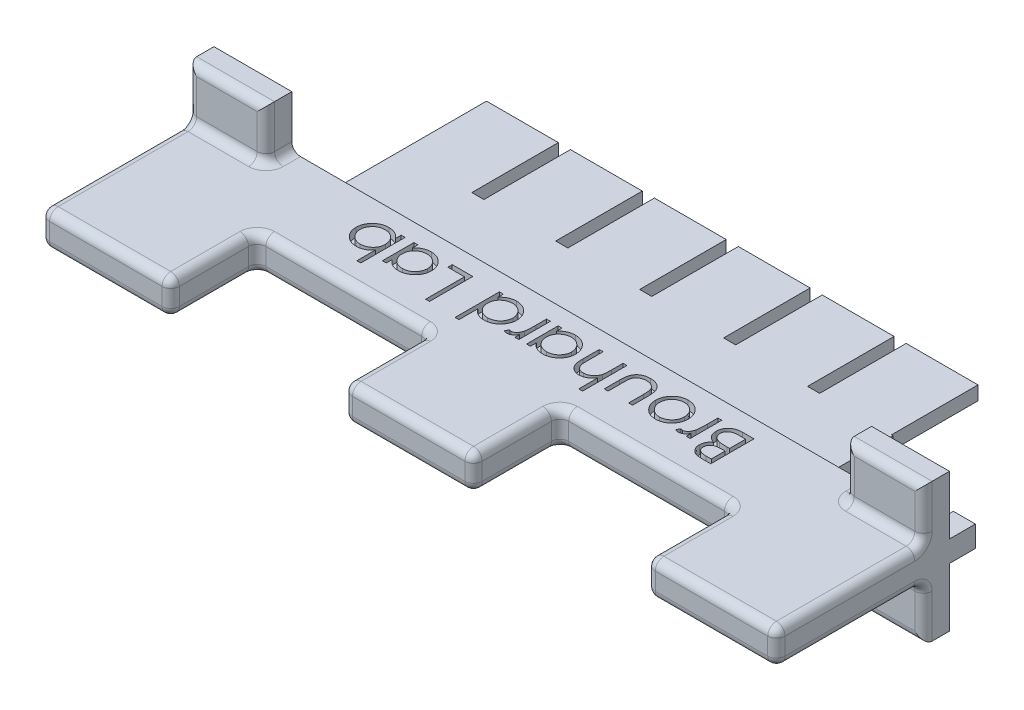
SolidWorks part; units mm, degrees
ref_plane "Front Plane" through (0, 0, 0) normal (0, 0, 1) x (1, 0, 0)
ref_plane "Top Plane" through (0, 0, 0) normal (0, 1, 0) x (1, 0, 0)
ref_plane "Right Plane" through (0, 0, 0) normal (1, 0, 0) x (0, 0, -1)
sketch "Sketch1" plane through (0, 0, 0) normal (0, 0, 1) x (1, 0, 0)
  line L1 (-42.5, 2) -> (42.5, 2)
  line L2 (-42.5, 2) -> (-42.5, -2)
  line L3 (-42.5, -2) -> (42.5, -2)
  line L4 (42.5, 2) -> (42.5, -2)
  line L5 (-42.5, 2) -> (42.5, -2) construction
  line L6 (-42.5, -2) -> (42.5, 2) construction
  point P0 (0, 0)
  dimension "D1" = 85
  dimension "D2" = 4
extrude "Boss-Extrude1" add sketch "Sketch1" along normal blind 10
sketch "Sketch2" plane through (0, 0, 10) normal (0, 0, 1) x (1, 0, 0)
  line L0 (-42.5, -2) -> (42.5, -2) construction
  line L1 (-42.5, 2) -> (-27.5, 2)
  line L2 (-42.5, 2) -> (-42.5, -2)
  line L3 (-42.5, -2) -> (-27.5, -2)
  line L4 (-27.5, 2) -> (-27.5, -2)
  line L6 (42.5, 2) -> (27.5, 2)
  line L7 (42.5, 2) -> (42.5, -2)
  line L8 (42.5, -2) -> (27.5, -2)
  line L9 (27.5, 2) -> (27.5, -2)
  line L10 (-7.5, 2) -> (7.5, 2)
  line L11 (-7.5, 2) -> (-7.5, -2)
  line L12 (-7.5, -2) -> (7.5, -2)
  line L13 (7.5, 2) -> (7.5, -2)
  line L14 (-7.5, 2) -> (7.5, -2) construction
  line L15 (-7.5, -2) -> (7.5, 2) construction
  point P12 (0, 0)
  dimension "D1" = 15
extrude "Boss-Extrude2" add sketch "Sketch2" along normal blind 10
sketch "Sketch3" plane through (0, 0, 0) normal (0, 0, -1) x (-1, 0, 0)
  line L9 (42.5, -1.225) -> (39.95, -1.225)
  line L10 (42.5, -1.225) -> (42.5, 1.225)
  line L11 (42.5, 1.225) -> (39.95, 1.225)
  line L12 (39.95, -1.225) -> (39.95, 1.225)
  line L13 (42.5, -1.225) -> (39.95, 1.225) construction
  line L14 (42.5, 1.225) -> (39.95, -1.225) construction
  line L15 (42.5, 2) -> (42.5, -2) construction
  line L16 (0, 0) -> (0, 13.9589)
  line L17 (-42.5, 1.225) -> (-39.95, -1.225) construction
  line L18 (-42.5, -1.225) -> (-39.95, 1.225) construction
  line L19 (-39.95, -1.225) -> (-39.95, 1.225)
  line L20 (-42.5, 1.225) -> (-39.95, 1.225)
  line L21 (-42.5, -1.225) -> (-42.5, 1.225)
  line L22 (-42.5, -1.225) -> (-39.95, -1.225)
  point P3 (42.5, 0)
  point P10 (41.225, 0)
  point P16 (-41.225, 0)
  line M3 (-42.5, 2) -> (-42.5, -2)
  dimension "D1" = 2.45
  dimension "D2" = 2.55
extrude "Boss-Extrude3" add sketch "Sketch3" along normal blind 3 contours L22 L19 L20 M3 | L12 L11 L10 L9
sketch "Sketch4" plane through (0, 0, 0) normal (0, 0, -1) x (-1, 0, 0)
  line L1 (28.5, -0.8) -> (-28.5, -0.8)
  line L2 (28.5, -0.8) -> (28.5, 0.8)
  line L3 (28.5, 0.8) -> (-28.5, 0.8)
  line L4 (-28.5, -0.8) -> (-28.5, 0.8)
  line L5 (28.5, -0.8) -> (-28.5, 0.8) construction
  line L6 (28.5, 0.8) -> (-28.5, -0.8) construction
  point P0 (0, 0)
  dimension "D1" = 1.6
  dimension "D2" = 57
extrude "Boss-Extrude4" add sketch "Sketch4" along normal blind 7.5
sketch "Sketch6" plane through (0, 0, 0) normal (0, 0, -1) x (-1, 0, 0)
  line L1 (42.5, -2) -> (33.5, -2)
  line L2 (42.5, -2) -> (42.5, -8)
  line L3 (42.5, -8) -> (33.5, -8)
  line L4 (33.5, -2) -> (33.5, -8)
  line L5 (42.5, 2) -> (33.5, 2)
  line L6 (42.5, 2) -> (42.5, 8)
  line L7 (42.5, 8) -> (33.5, 8)
  line L8 (33.5, 2) -> (33.5, 8)
  line L9 (-42.5, -2) -> (-33.5, -2)
  line L10 (-42.5, -2) -> (-42.5, -8)
  line L11 (-42.5, -8) -> (-33.5, -8)
  line L12 (-33.5, -2) -> (-33.5, -8)
  line L13 (-42.5, 2) -> (-33.5, 2)
  line L14 (-42.5, 2) -> (-42.5, 8)
  line L15 (-42.5, 8) -> (-33.5, 8)
  line L16 (-33.5, 2) -> (-33.5, 8)
  dimension "D1" = 6
  dimension "D2" = 9
extrude "Boss-Extrude6" add sketch "Sketch6" against normal blind 3
fillet "Fillet1" radius 1 52 edges at (-42.5, -2, 11.5) (-33.5, -2, 1.5) (-38, -2, 3) (-33.5, -5, 3) (-38, -8, 3) (-42.5, -5, 3) (-27.5, 0, 20) (-35, -2, 20) (-42.5, 0, 20) (-35, 2, 20) (33.5, -2, 1.5) (42.5, -2, 11.5) (42.5, 2, 11.5) (33.5, 2, 1.5) (-33.5, 2, 1.5) (-42.5, 2, 11.5) (38, -8, 3) (33.5, -5, 3) (38, -2, 3) (42.5, -5, 3) (35, -2, 20) (27.5, 0, 20) (35, 2, 20) (42.5, 0, 20) (38, 2, 3) (33.5, 5, 3) (38, 8, 3) (42.5, 5, 3) (0, -2, 20) (-7.5, 0, 20) (0, 2, 20) (7.5, 0, 20) (-38, 8, 3) (-33.5, 5, 3) (-38, 2, 3) (-42.5, 5, 3) (27.5, 2, 15) (27.5, -2, 15) (27.5, 0, 10) (17.5, -2, 10) (17.5, 2, 10) (7.5, -2, 15) (7.5, 2, 15) (7.5, 0, 10) (-7.5, 2, 15) (-7.5, -2, 15) (-27.5, -2, 15) (-27.5, 2, 15) (-27.5, 0, 10) (-17.5, 2, 10) (-7.5, 0, 10) (-17.5, -2, 10)
ref_plane "Plane1" through (0, 0, 0) normal (0, 1, 0) x (1, 0, 0)
sketch "Sketch7" plane through (0, 2, 0) normal (0, 1, 0) x (1, 0, 0)
  line L0 (30.9142, -2.045) -> (-30.9142, -2.045)
  line L1 (32.5, 0) -> (-32.5, 0) construction
  point P2 (0, -2.045)
  point P5 (0, 0)
sketch "Sketch8" plane through (0, 2, 0) normal (0, 1, 0) x (1, 0, 0)
  text T0 "Brouhard Lab" font "Century Gothic" height 5
extrude "Cut-Extrude1" cut sketch "Sketch8" against normal blind 1
sketch "Sketch5" plane through (0, 0, -7.5) normal (0, 0, -1) x (-1, 0, 0)
  line L0 (28.5, 0.8) -> (-28.5, 0.8) construction
  line L1 (28.5, -0.8) -> (20.2, -0.8)
  line L2 (28.5, -0.8) -> (28.5, 0.8)
  line L3 (28.5, 0.8) -> (20.2, 0.8)
  line L4 (20.2, -0.8) -> (20.2, 0.8)
  line L97 (18.8, -0.8) -> (10.5, -0.8)
  line L98 (18.8, -0.8) -> (18.8, 0.8)
  line L99 (18.8, 0.8) -> (10.5, 0.8)
  line L100 (10.5, -0.8) -> (10.5, 0.8)
  line L101 (9.1, -0.8) -> (0.8, -0.8)
  line L102 (9.1, -0.8) -> (9.1, 0.8)
  line L103 (9.1, 0.8) -> (0.8, 0.8)
  line L104 (0.8, -0.8) -> (0.8, 0.8)
  line L105 (-0.6, -0.8) -> (-8.9, -0.8)
  line L106 (-0.6, -0.8) -> (-0.6, 0.8)
  line L107 (-0.6, 0.8) -> (-8.9, 0.8)
  line L108 (-8.9, -0.8) -> (-8.9, 0.8)
  line L109 (-10.3, -0.8) -> (-18.6, -0.8)
  line L110 (-10.3, -0.8) -> (-10.3, 0.8)
  line L111 (-10.3, 0.8) -> (-18.6, 0.8)
  line L112 (-18.6, -0.8) -> (-18.6, 0.8)
  line L113 (-20, -0.8) -> (-28.3, -0.8)
  line L114 (-20, -0.8) -> (-20, 0.8)
  line L115 (-20, 0.8) -> (-28.3, 0.8)
  line L116 (-28.3, -0.8) -> (-28.3, 0.8)
  dimension "D2" = 8.3
  dimension "D1" = 6
extrude "Boss-Extrude5" add sketch "Sketch5" along normal blind 10
